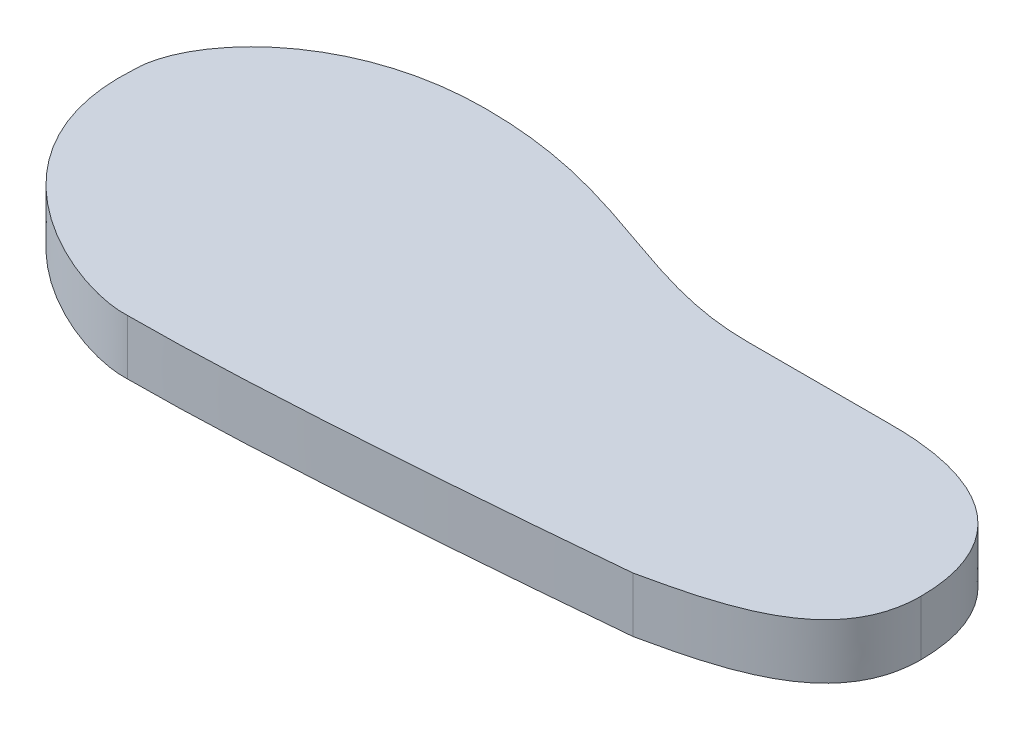
SolidWorks part; units mm, degrees
ref_plane "Front Plane" through (0, 0, 0) normal (0, 0, 1) x (1, 0, 0)
ref_plane "Top Plane" through (0, 0, 0) normal (0, 1, 0) x (1, 0, 0)
ref_plane "Right Plane" through (0, 0, 0) normal (1, 0, 0) x (0, 0, -1)
sketch "Sketch1" plane through (0, 0, 0) normal (0, 1, 0) x (1, 0, 0)
  line L0 (0, 0) -> (29.8, 0) construction
  line L1 (0, 0) -> (0, 24.3) construction
  line L2 (0, 0) -> (0, -22.5) construction
  line L3 (0, 0) -> (-86.5, 0) construction
  line L4 (-26, 0) -> (-26, 24.3) construction
  line L5 (-86.5, 0) -> (-86.5, 37.2) construction
  line L6 (-86.5, 11.6) -> (-124.6, 11.6) construction
  line L7 (-86.5, 0) -> (-86.5, -27.9) construction
  dimension "D1" = 29.8
  dimension "D2" = 24.3
  dimension "D3" = 22.5
  dimension "D4" = 26
  dimension "D5" = 86.5
  dimension "D6" = 27.9
  dimension "D7" = 37.2
  dimension "D8" = 11.6
  dimension "D9" = 38.1
sketch "Sketch2" plane through (0, 0, 0) normal (0, 1, 0) x (1, 0, 0)
  line L0 (-26, 24.3) -> (0, 24.3)
  line L1 (-124.6, 0.1449) -> (-124.6, 23.0551) construction
  line L2 (-106.5667, 37.2) -> (-66.4333, 37.2) construction
  line L3 (-42.2984, 24.3) -> (-9.7006, 24.3) construction
  line L4 (-107.4998, 37.2) -> (-65.4572, 37.2) construction
  line L5 (-64.2941, -27.9) -> (-108.7059, -27.9) construction
  line L6 (29.8, -11.2792) -> (29.8, 11.2792) construction
  line L7 (29.8, -14.0147) -> (29.8, 14.0918) construction
  spline S0 degree 3 poles (-26, 24.3) (-46.3736, 24.3) (-60.2234, 37.2) (-86.5, 37.2) knots 0 0 0 0 1 1 1 1
  spline S1 degree 3 poles (-86.5, 37.2) (-111.5833, 37.2) (-124.6, 21.1459) (-124.6, 11.6) knots 0 0 0 0 1 1 1 1
  spline S2 degree 3 poles (0, 24.3) (20.6838, 24.3847) (29.8, 14.099) (29.8, 0) knots 0 0 0 0 1 1 1 1
  spline S3 degree 3 poles (29.8, 0) (29.8, -15.9034) (12.7938, -19.6737) (0, -22.5) knots 0 0 0 0 1 1 1 1
  spline S4 degree 2 poles (-86.5, -27.9) (-58.7426, -27.9) (0, -22.5) knots 0 0 0 1 1 1
  spline S5 degree 3 poles (-124.6, 11.6) (-126.6455, -15.9296) (-96.1692, -28.4589) (-86.5, -27.9) knots 0 0 0 0 1 1 1 1
  point P0 (0, 24.3)
  point P2 (29.8, 0)
  point P4 (0, -22.5)
  point P6 (-26, 24.3)
  point P8 (-86.5, 37.2)
  point P10 (-124.6, 11.6)
  point P12 (-86.5, -27.9)
extrude "Boss-Extrude1" add sketch "Sketch2" along normal blind 10
